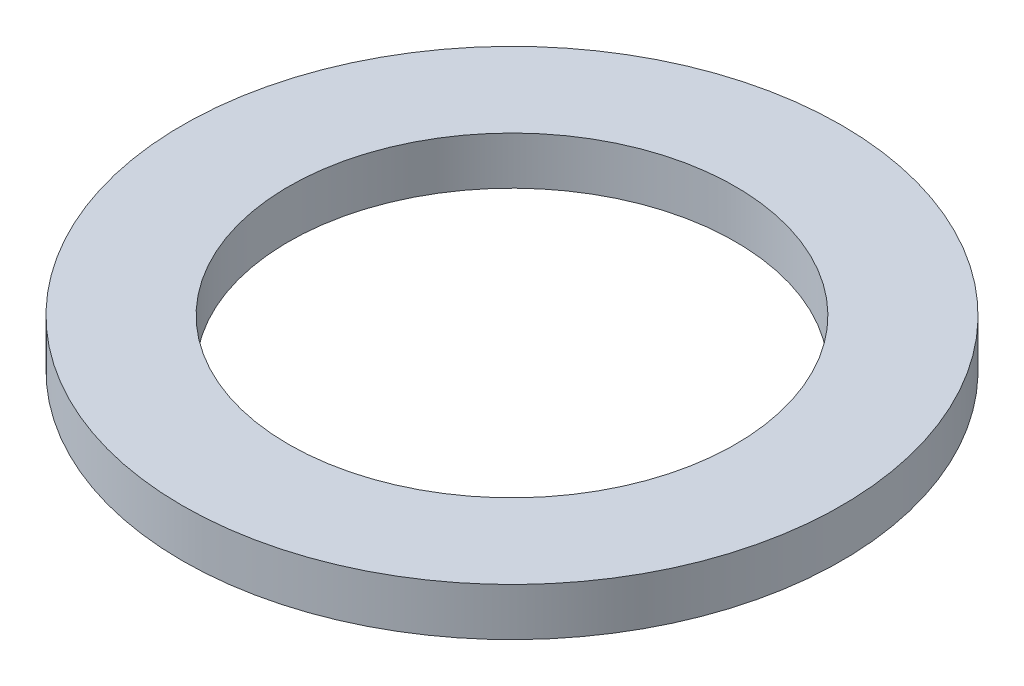
SolidWorks part; units mm, degrees
ref_plane "Front Plane" through (0, 0, 0) normal (0, 0, 1) x (1, 0, 0)
ref_plane "Top Plane" through (0, 0, 0) normal (0, 1, 0) x (1, 0, 0)
ref_plane "Right Plane" through (0, 0, 0) normal (1, 0, 0) x (0, 0, -1)
sketch "Sketch1" plane through (0, 0, 0) normal (0, 1, 0) x (1, 0, 0)
  circle A0 centre (0, 0) radius 9.4615
  dimension "OD" = 18.923
extrude "Boss-Extrude1" add sketch "Sketch1" along normal blind 1.3716
sketch "Sketch5" plane through (0, 1.3716, 0) normal (0, 1, 0) x (-1, 0, 0)
  circle A0 centre (0, 0) radius 6.4135
  dimension "ID" = 12.827
extrude "Cut-Extrude1" cut sketch "Sketch5" against normal through all
